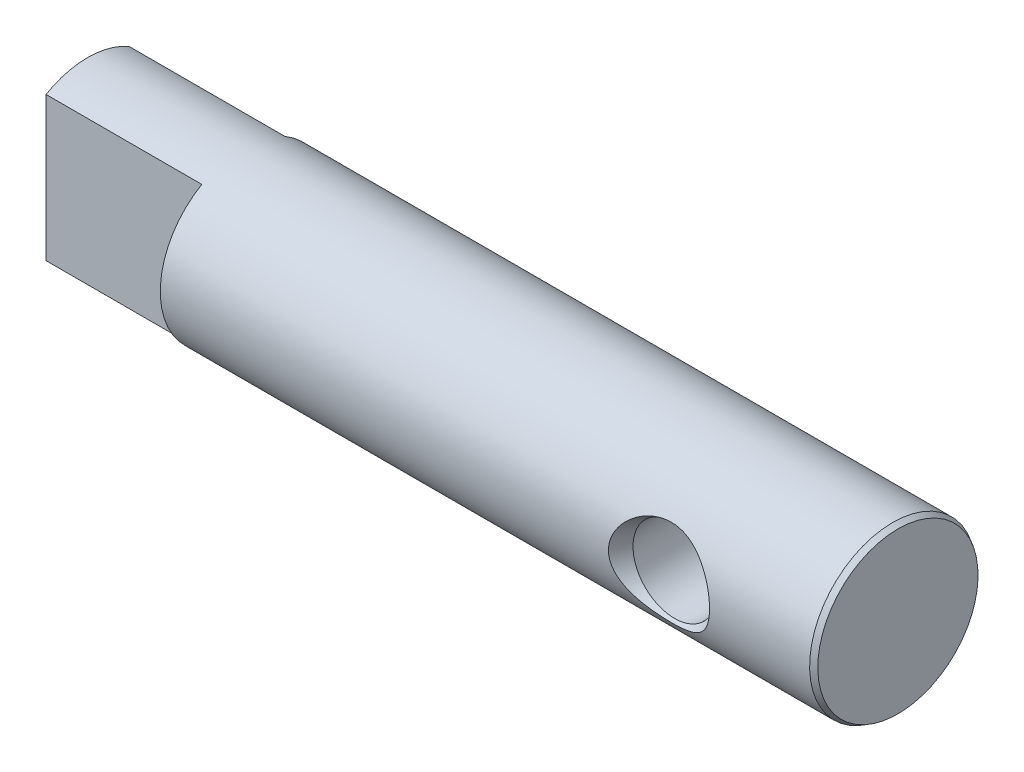
SolidWorks part; units mm, degrees
material "1.4301 (X5CrNi18-10)"
ref_plane "Vorne" through (0, 0, 0) normal (0, 0, 1) x (1, 0, 0)
ref_plane "Oben" through (0, 0, 0) normal (0, 1, 0) x (1, 0, 0)
ref_plane "Rechts" through (0, 0, 0) normal (1, 0, 0) x (0, 0, -1)
sketch "Skizze2" plane through (0, 0, 0) normal (0, 0, 1) x (1, 0, 0)
  line L0 (0, -8.8) -> (0, 8.8) construction
  line L1 (14.5, 8) -> (-63, 8)
  line L2 (15, 7.7113) -> (15, 0)
  line L3 (15, 0) -> (-63, 0)
  line L4 (-63, 8) -> (-63, 0)
  line L5 (14.5, 8) -> (15, 7.7113)
  circle A0 centre (0, 0) radius 4
  dimension "D1" = 8
  dimension "D2" = 15
  dimension "D3" = 8
  dimension "D4" = 63
  dimension "D5" = 30
  dimension "D6" = 0.5
revolve "Rotation1" add sketch "Skizze2" angle 360 about L3
sketch "Skizze3" plane through (0, 0, 0) normal (0, 1, 0) x (1, 0, 0)
  line L0 (-4.866, 8) -> (-4, 6.5)
  line L1 (-4, 6.5) -> (-4, -6.5)
  line L2 (-4, -6.5) -> (-4.866, -8)
  line L3 (-63, -8) -> (14.5, -8) construction
  line L4 (-4.866, -8) -> (0, -8)
  line L5 (0, -8) -> (0, 8)
  line L6 (14.5, 8) -> (-63, 8) construction
  line L7 (0, 8) -> (-4.866, 8)
  line L8 (0, -8.8) -> (0, 8.8) construction
  dimension "D1" = 30
  dimension "D2" = 30
  dimension "D3" = 1.5
  dimension "D4" = 1.5
  dimension "D5" = 4
revolve "Schnitt-Rotation1" cut sketch "Skizze3" angle 360 about L5
sketch "Skizze5" plane through (-63, 0, 0) normal (-1, 0, 0) x (0, 0, 1)
  line L1 (-4, 10) -> (4, 10)
  line L2 (-4, 10) -> (-4, -10)
  line L3 (-4, -10) -> (4, -10)
  line L4 (4, 10) -> (4, -10)
  dimension "D1" = 8
  dimension "D2" = 20
  dimension "D3" = 10
  dimension "D4" = 4
extrude "Schnitt-Linear austragen1" cut sketch "Skizze5" against normal blind 15 flip side to cut
hole_wizard "M3 Gewindebohrung1" positions "Skizze7" profile "Skizze6" tap size "M3" standard "DIN"
sketch "Skizze7" plane through (-63, 0, 0) normal (-1, 0, 0) x (0, 0, 1)
  point P0 (0, 0)
sketch "Skizze6" plane through (-63, 0, 0) normal (0, 1, 0) x (0, 0, 1)
  line L0 (0, 0) -> (0, 9.2511)
  line L1 (0, 9.2511) -> (1.25, 8.5)
  line L2 (1.25, 8.5) -> (1.25, 0)
  line L5 (1.25, 0) -> (0, 0)
  line L10 (0, 9.2511) -> (-1.25, 8.5) construction
  line L11 (0, -6.35) -> (0, 107.95) construction
  dimension "Bohrerdurchmesser" = 2.5
  dimension "Bohrungstiefe" = 8.5
  dimension "Spitzenwinkel" = 118
cosmetic thread "Bohrungsgewinde1" parameters "D1"=6, "D2"=3
equation "\"D3@Skizze3\"=\"D4@Skizze3\""
equation "\"D2@Skizze3\"=\"D1@Skizze3\""
